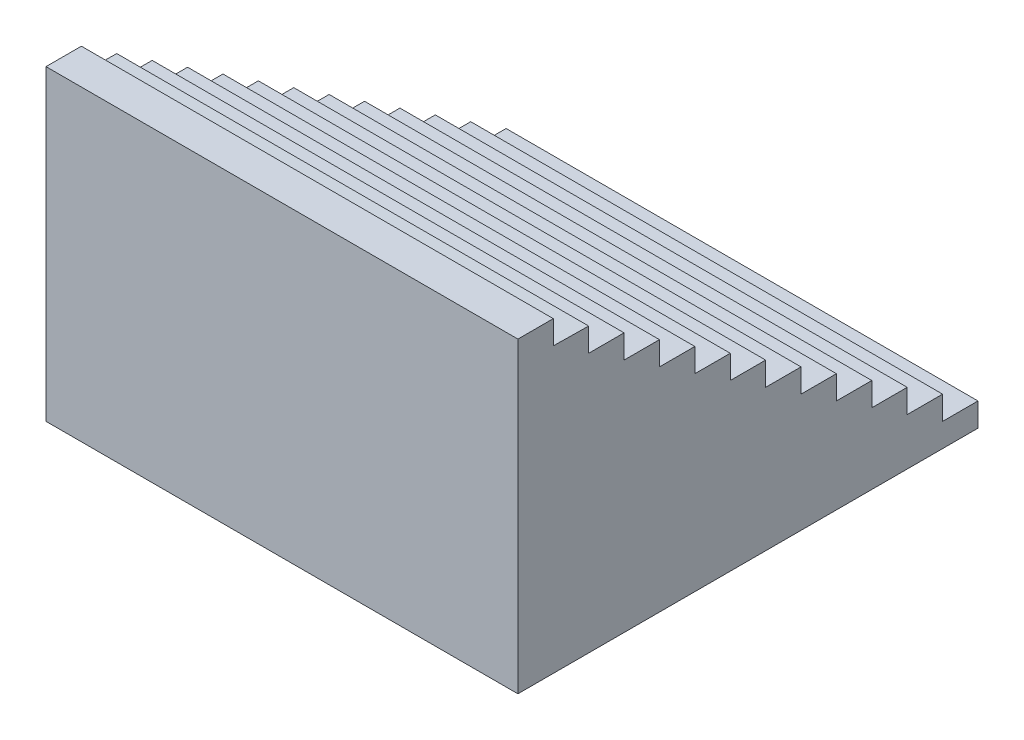
SolidWorks part; units mm, degrees
ref_plane "Front Plane" through (0, 0, 0) normal (0, 0, 1) x (1, 0, 0)
ref_plane "Top Plane" through (0, 0, 0) normal (0, 1, 0) x (1, 0, 0)
ref_plane "Right Plane" through (0, 0, 0) normal (1, 0, 0) x (0, 0, -1)
sketch "Sketch1" plane through (0, 0, 0) normal (1, 0, 0) x (0, 0, -1)
  line L0 (-75, 65.2131) -> (-60, 65.2131)
  line L1 (-60, 65.2131) -> (-60, 55.2131)
  line L2 (-60, 55.2131) -> (-45.0015, 55)
  line L7 (-45.0015, 55) -> (-45.0015, 45)
  line L8 (-45.0015, 45) -> (-30.0015, 45)
  line L9 (-30.0015, 45) -> (-30.0015, 35)
  line L10 (-30.0015, 35) -> (-15.0015, 35)
  line L11 (-15.0015, 35) -> (-15.0015, 25)
  line L12 (-15.0015, 25) -> (-0.0015, 25)
  line L13 (-0.0015, 25) -> (-0.0015, 15)
  line L14 (-0.0015, 15) -> (14.9985, 15)
  line L15 (14.9985, 15) -> (14.9985, 5)
  line L16 (14.9985, 5) -> (29.9985, 5)
  line L17 (29.9985, 5) -> (29.9985, -5)
  line L18 (29.9985, -5) -> (44.9985, -5)
  line L19 (44.9985, -5) -> (44.9985, -15)
  line L20 (44.9985, -15) -> (59.9985, -15)
  line L21 (59.9985, -15) -> (59.9985, -25)
  line L22 (59.9985, -25) -> (74.9985, -25)
  line L23 (74.9985, -25) -> (74.9985, -35)
  line L24 (74.9985, -35) -> (89.9985, -35)
  line L25 (89.9985, -35) -> (89.9985, -45)
  line L26 (89.9985, -45) -> (104.9985, -45)
  line L27 (104.9985, -45) -> (104.9985, -55)
  line L28 (104.9985, -55) -> (119.9985, -55)
  line L29 (119.9985, -55) -> (119.9985, -65)
  line L30 (-75, 65.2131) -> (-75, -65)
  line L31 (-75, 65.2131) -> (119.9985, 65.2131) construction
  line L32 (-75, 65.2131) -> (-75, -65) construction
  line L33 (-75, -65) -> (119.9985, -65) construction
  line L34 (119.9985, 65.2131) -> (119.9985, -65) construction
  line L35 (-75, -65) -> (119.9985, -65)
  point P4 (0, 0)
  dimension "D3" = 15
  dimension "D4" = 10
extrude "Boss-Extrude1" add sketch "Sketch1" against normal blind 200
